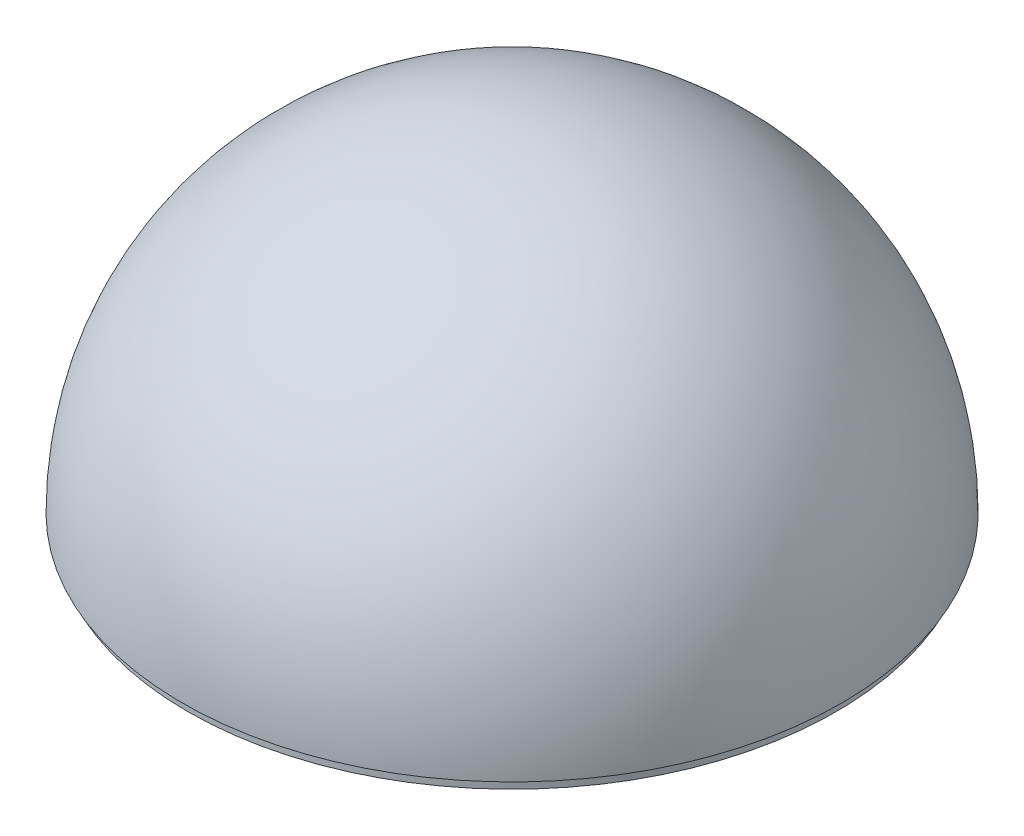
SolidWorks part; units mm, degrees
ref_plane "Front Plane" through (0, 0, 0) normal (0, 0, 1) x (1, 0, 0)
ref_plane "Top Plane" through (0, 0, 0) normal (0, 1, 0) x (1, 0, 0)
ref_plane "Right Plane" through (0, 0, 0) normal (1, 0, 0) x (0, 0, -1)
sketch "Sketch1" plane through (0, 0, 0) normal (0, 1, 0) x (1, 0, 0)
  line L0 (0, 152.4) -> (0, -152.4)
  arc A0 (0, -152.4) -> (0, 152.4) centre (0, 0) ccw
  dimension "D1" = 304.8
revolve "Revolve1" add sketch "Sketch1" angle 180 about L0
shell "Shell1" thickness 2.54
sketch "Sketch2" plane through (0, 0, 0) normal (0, 1, 0) x (1, 0, 0)
  circle A0 centre (0, 0) radius 152.4
  dimension "D1" = 304.8
extrude "Boss-Extrude1" add sketch "Sketch2" against normal blind 4.7625 separate body
sketch "Sketch3" plane through (0, -4.7625, 0) normal (0, -1, 0) x (1, 0, 0)
  line L0 (0, 0) -> (0, 152.4) construction
  line L1 (0, 0) -> (152.4, 0) construction
  circle A0 centre (0, 0) radius 152.4 construction
  circle A1 centre (0, 0) radius 152.4 construction
